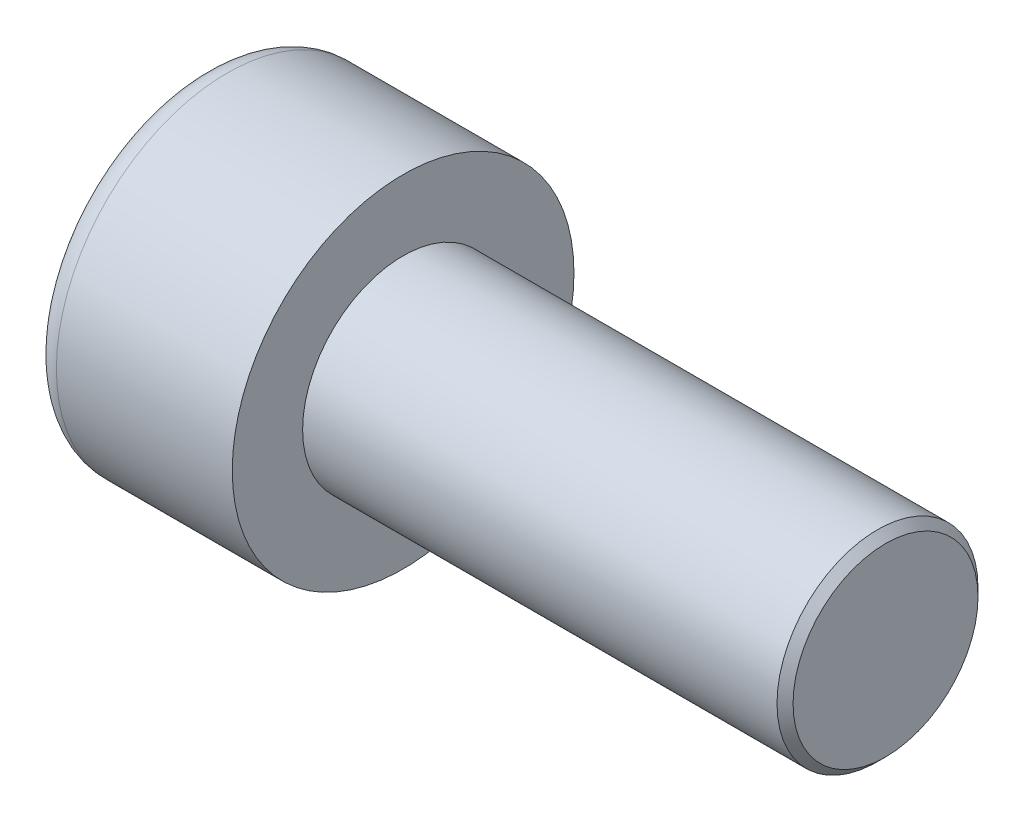
SolidWorks part; units mm, degrees
ref_plane "Front" through (0, 0, 0) normal (0, 0, 1) x (1, 0, 0)
ref_plane "Top" through (0, 0, 0) normal (0, 1, 0) x (1, 0, 0)
ref_plane "Right" through (0, 0, 0) normal (1, 0, 0) x (0, 0, -1)
sketch "Sketch1" plane through (0, 0, 0) normal (1, 0, 0) x (0, 0, -1)
  circle A0 centre (0, 0) radius 4.25
  dimension "dk" = 8.5
extrude "BaseHead" add sketch "Sketch1" along normal blind 5
sketch "Sketch2" plane through (5, 0, 0) normal (1, 0, 0) x (0, 0, -1)
  circle A0 centre (0, 0) radius 2.5
  dimension "d" = 5
extrude "BaseBody" add sketch "Sketch2" along normal blind 12
cosmetic thread "ThreadCosmetic1" [suppressed] parameters "b"=22, "D2"=4.134
sketch "Sketch3" plane through (0, 0, 0) normal (1, 0, 0) x (0, 0, -1)
  line L1 (2.3094, 0) -> (1.1547, 2)
  line L2 (1.1547, 2) -> (-1.1547, 2)
  line L3 (-1.1547, 2) -> (-2.3094, 0)
  line L4 (-2.3094, 0) -> (-1.1547, -2)
  line L5 (-1.1547, -2) -> (1.1547, -2)
  line L6 (1.1547, -2) -> (2.3094, 0)
  circle A0 centre (0, 0) radius 2 construction
  dimension "s" = 4
  dimension "e" = 4.6188
extrude "HexagonSocket" cut sketch "Sketch3" along normal blind 2.5
sketch "Sketch4" plane through (-4.1961, 0.75, 0) normal (0, 0, 1) x (-1, 0, 0)
  line L0 (-6.6961, 2.75) -> (-7.8508, 0.75)
  line L2 (-7.8508, 0.75) -> (-6.6961, 0.75)
  line L3 (-6.6961, 0.75) -> (-6.6961, 2.75)
  line L4 (-5.0351, 0.75) -> (0.839, 0.75) construction
  line L5 (-21.1961, 0.75) -> (-9.1961, 0.75) construction
  line L6 (-9.1961, 0.75) -> (-4.1961, 0.75) construction
  dimension "m" = 60
revolve "Cut-Revolve1" cut sketch "Sketch4" angle 360 about L4
fillet "HeadFillet" [suppressed] radius 0.2
fillet "TopFillet" radius 0.625 1 edges at (0, 0, -4.25)
chamfer "Chamfer1" distance 0.2 angle 45 1 edges at (17, 0, -2.5)
sketch "Sketch5" plane through (0, 0, 0) normal (0, 0, 1) x (1, 0, 0)
  line L0 (16.8, 2.125) -> (17.0165, 2.5)
  line L1 (17.0165, 2.5) -> (17.0165, 2.933)
  line L2 (17.0165, 2.933) -> (16.5835, 2.933)
  line L3 (16.5835, 2.933) -> (16.5835, 2.5)
  line L4 (16.5835, 2.5) -> (16.8, 2.125)
  line L5 (0, 0) -> (7.8886, 0) construction
  line L6 (16.8, -2.5) -> (16.8, 2.5) construction
  dimension "D1" = 5
  dimension "D2" = 0.433
revolve "Cut-Revolve10" [suppressed] cut sketch "Sketch5" angle 360 about L5
pattern_linear "LPattern10" [suppressed] count 42 spacing 0.5196 along (1, 0, 0)
equation "\"r1@TopFillet\" = \"d@Sketch2\" / 8"
equation "\"D1@Chamfer1\" = \"r@HeadFillet\""
equation "\"D1@Sketch5\" = \"d@Sketch2\""
equation "\"D2@Sketch5\" =  ( \"d@Sketch2\" - \"D2@ThreadCosmetic1\" )  / 2"
equation "\"D3@LPattern10\" = \"D2@Sketch5\" * 1.2"
equation "\"D1@LPattern10\" = \"b@ThreadCosmetic1\" / \"D3@LPattern10\""
